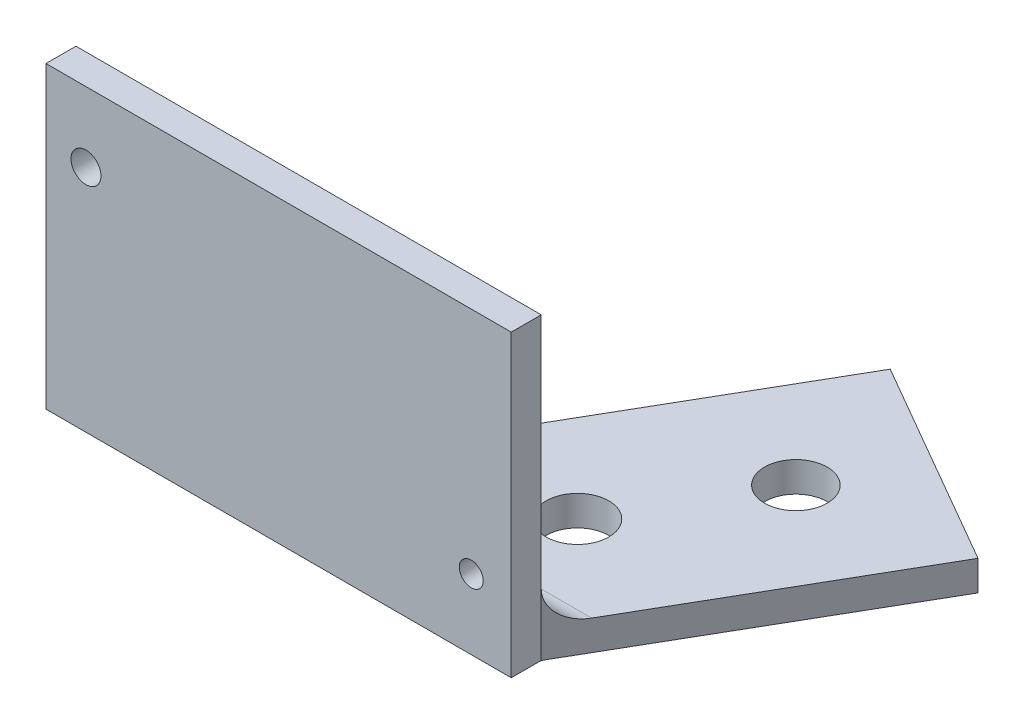
SolidWorks part; units mm, degrees
ref_plane "Front Plane" through (0, 0, 0) normal (0, 0, 1) x (1, 0, 0)
ref_plane "Top Plane" through (0, 0, 0) normal (0, 1, 0) x (1, 0, 0)
ref_plane "Right Plane" through (0, 0, 0) normal (1, 0, 0) x (0, 0, -1)
sketch "Sketch1" plane through (0, 0, 0) normal (0, 0, 1) x (1, 0, 0)
  line L1 (0, 0) -> (33.782, 0) construction
  line L2 (0, 0) -> (0, 19.812) construction
  line L3 (0, 19.812) -> (33.782, 19.812) construction
  line L4 (33.782, 0) -> (33.782, 19.812) construction
  line L5 (-1.5875, -1.5875) -> (35.3695, -1.5875)
  line L6 (-1.5875, -1.5875) -> (-1.5875, 19.812)
  line L7 (-1.5875, 19.812) -> (35.3695, 19.812)
  line L8 (35.3695, -1.5875) -> (35.3695, 19.812)
  circle A0 centre (1.5875, 14.2558) radius 1.1906
  circle A1 centre (32.1945, 1.5875) radius 0.9525
  dimension "D3" = 2.3813
  dimension "D4" = 1.905
  dimension "D5" = 1.5875
  dimension "D6" = 1.5875
  dimension "D7" = 1.5875
  dimension "D8" = 5.5562
  dimension "D9" = 3.175
  dimension "D11" = 3.175
  dimension "D12" = 5.5562
  dimension "D1" = 19.812
  dimension "D2" = 33.782
  dimension "D10" = 3.175
extrude "Boss-Extrude1" add sketch "Sketch1" along normal blind 2.3813
sketch "Sketch2" plane through (0, -1.5875, 0) normal (0, -1, 0) x (1, 0, 0)
  line L8 (-1.5875, 0) -> (35.3695, 0) construction
  line L9 (-1.5875, 2.3813) -> (35.3695, 2.3813)
  line L10 (-1.5875, 2.3813) -> (-1.5875, 0)
  line L12 (35.3695, 2.3813) -> (35.3695, 0)
  line L15 (48.0695, -21.997) -> (31.5717, -31.522)
  line L17 (48.0695, -21.997) -> (35.3695, 0)
  line L19 (31.5717, -31.522) -> (13.3725, 0)
  line L20 (13.3725, 0) -> (-1.5875, 0)
  dimension "D1" = 19.05
  dimension "D2" = 25.4
  dimension "D3" = 60
extrude "Boss-Extrude3" add sketch "Sketch2" along normal blind 2.3813
sketch "Sketch4" plane through (0, -1.5875, 0) normal (0, 1, 0) x (1, 0, 0)
  line L0 (39.8206, 26.7595) -> (35.801, 19.7973) construction
  line L2 (35.801, 19.7973) -> (29.451, 8.7988) construction
  line L3 (29.451, 8.7988) -> (24.371, 0) construction
  line L5 (48.0695, 21.997) -> (31.5717, 31.522) construction
  line L6 (35.3695, 0) -> (13.3725, 0) construction
  circle A0 centre (35.801, 19.7973) radius 2.4892
  circle A1 centre (29.451, 8.7988) radius 2.4892
  point P10 (24.371, 0)
  point P15 (39.8206, 26.7595)
  dimension "D1" = 4.9784
  dimension "D2" = 12.7
  dimension "D3" = 10.16
extrude "Cut-Extrude2" cut sketch "Sketch4" against normal up to next
fillet "Fillet1" radius 2.54 1 edges at (24.371, -1.5875, 0)
